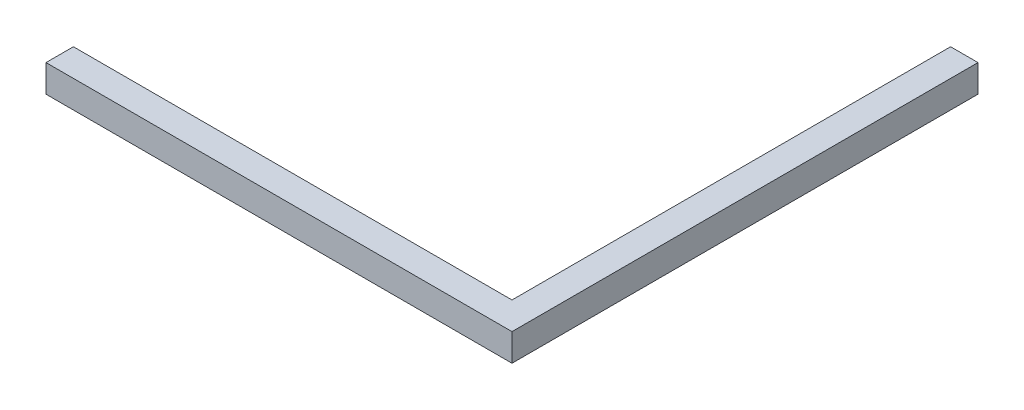
SolidWorks part; units mm, degrees
ref_plane "Front Plane" through (0, 0, 0) normal (0, 0, 1) x (1, 0, 0)
ref_plane "Top Plane" through (0, 0, 0) normal (0, 1, 0) x (1, 0, 0)
ref_plane "Right Plane" through (0, 0, 0) normal (1, 0, 0) x (0, 0, -1)
sketch "Sketch1" plane through (0, 0, 0) normal (0, 1, 0) x (1, 0, 0)
  line L0 (-85, 85) -> (85, -85) construction
  line L1 (-85, 85) -> (85, 85) construction
  line L2 (-85, 85) -> (-85, -85) construction
  line L3 (-85, -85) -> (85, -85) construction
  line L4 (85, 85) -> (85, -85) construction
  line L5 (-85, -85) -> (85, -85)
  line L6 (85, -85) -> (85, 85)
  line L7 (85, 85) -> (75, 85)
  line L8 (75, 85) -> (75, -75)
  line L9 (75, -75) -> (-85, -75)
  line L10 (-85, -75) -> (-85, -85)
  dimension "D1" = 170
  dimension "D2" = 170
  dimension "D3" = 10
  dimension "D4" = 10
extrude "Boss-Extrude1" add sketch "Sketch1" along normal blind 10
